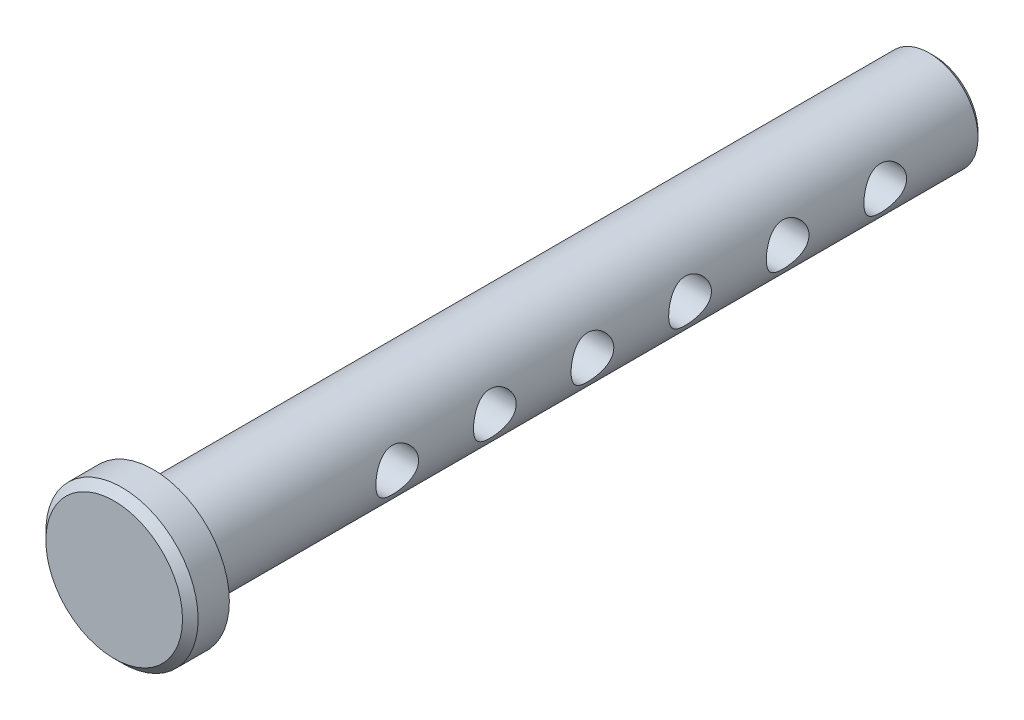
SolidWorks part; units mm, degrees
material "Cast Alloy Steel"
ref_plane "Front" through (0, 0, 0) normal (0, 0, 1) x (1, 0, 0)
ref_plane "Top" through (0, 0, 0) normal (0, 1, 0) x (1, 0, 0)
ref_plane "Right" through (0, 0, 0) normal (1, 0, 0) x (0, 0, -1)
sketch "Sketch1" plane through (0, 0, 0) normal (0, 0, 1) x (1, 0, 0)
  circle A0 centre (0, 0) radius 3.175
  point P3 (0, 3.175)
  point P4 (0, -3.175)
  dimension "dia" = 6.35
extrude "Extrude1" add sketch "Sketch1" along normal mid plane 50.8
sketch "Sketch2" plane through (0, 0, 25.4) normal (0, 0, 1) x (1, 0, 0)
  circle A0 centre (0, 0) radius 4.953
  dimension "head dia" = 9.906
extrude "Extrude2" add sketch "Sketch2" along normal blind 2.54
chamfer "Chamfer1" distance 0.508 angle 45 1 edges at (4.953, 0, 27.94)
sketch "Sketch3" plane through (0, 0, 0) normal (1, 0, 0) x (0, 0, -1)
  line L1 (25.4, -3.175) -> (25.4, 3.175) construction
  circle A0 centre (19.05, 0) radius 1.3891
  point P2 (17.6609, 0)
  dimension "D1" = 6.35
  dimension "hole dia" = 2.7781
extrude "Extrude3" cut sketch "Sketch3" against normal through all and the other way through all
pattern_linear "LPattern1" count 6 spacing 6.35 along (0, 0, 1) of "Extrude3"
chamfer "Chamfer2" distance 0.3175 angle 45 1 edges at (3.175, 0, -25.4)
ref_plane "Plane1" through (0, 0, -19.05) normal (0, 0, 1) x (1, 0, 0)
sketch "Sketch8" plane through (0, 0, 0) normal (1, 0, 0) x (0, 0, -1)
  line L0 (-27.94, 4.445) -> (-27.94, -4.445) construction
  line L1 (-27.432, -4.953) -> (-25.4, -4.953) construction
  line L2 (25.4, -2.8575) -> (25.4, 2.8575) construction
  circle A0 centre (12.7, 0) radius 1.3891 construction
  circle A1 centre (19.05, 0) radius 1.3891 construction
  point P0 (-27.94, 4.953)
  point P1 (-25.4, 4.953)
  point P5 (25.4, 3.175)
  point P8 (-27.94, -4.953)
  point P9 (25.4, -3.175)
  point P12 (19.05, 0)
  point P13 (12.7, 0)
  point P17 (12.7, -1.3891)
  point P19 (19.05, -1.3891)
equation "\"D1@Chamfer1\" = \"head ht@Extrude2\" * .2"
equation "\"D1@Chamfer2\" = \"dia@Sketch1\" * .05"
